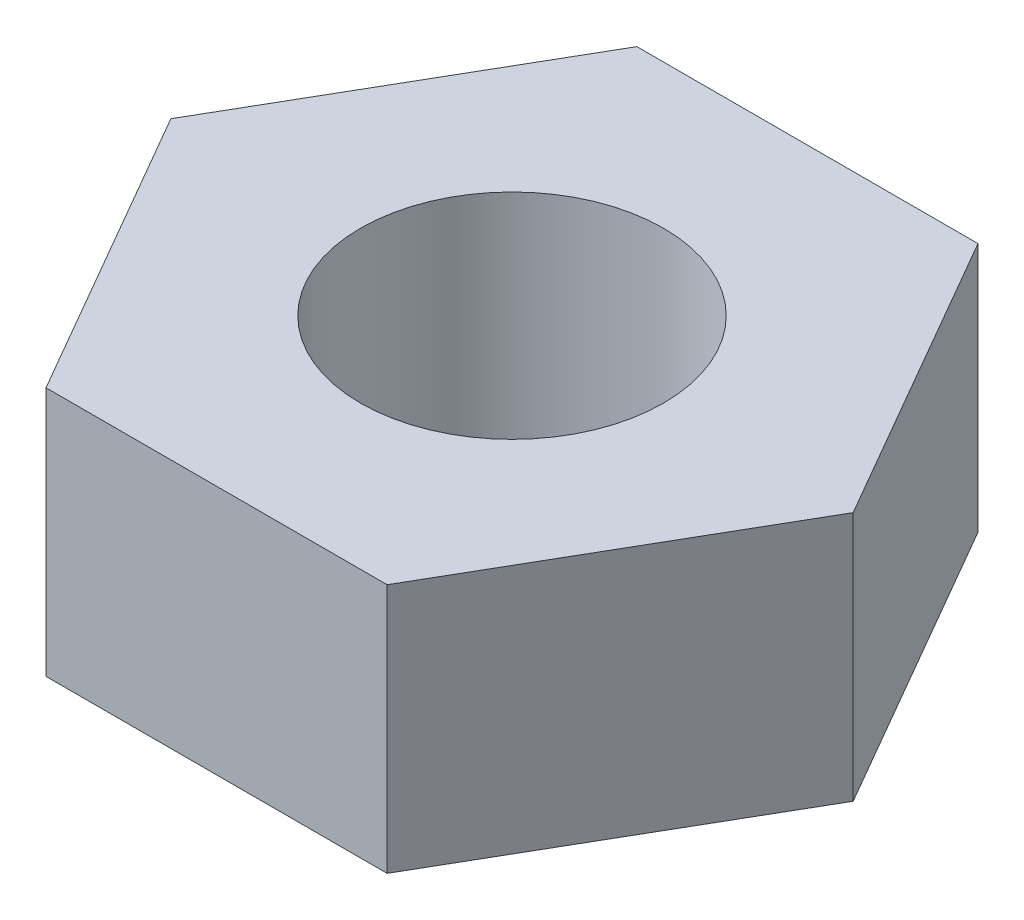
SolidWorks part; units mm, degrees
material "1060 Alloy"
ref_plane "Front Plane" through (0, 0, 0) normal (0, 0, 1) x (1, 0, 0)
ref_plane "Top Plane" through (0, 0, 0) normal (0, 1, 0) x (1, 0, 0)
ref_plane "Right Plane" through (0, 0, 0) normal (1, 0, 0) x (0, 0, -1)
sketch "Sketch1" plane through (0, 0, 0) normal (0, 1, 0) x (1, 0, 0)
  line L1 (2.2517, 0) -> (1.1258, 1.95)
  line L2 (1.1258, 1.95) -> (-1.1258, 1.95)
  line L3 (-1.1258, 1.95) -> (-2.2517, 0)
  line L4 (-2.2517, 0) -> (-1.1258, -1.95)
  line L5 (-1.1258, -1.95) -> (1.1258, -1.95)
  line L6 (1.1258, -1.95) -> (2.2517, 0)
  circle A0 centre (0, 0) radius 1
  circle A1 centre (0, 0) radius 1.95 construction
  point P3 (2.0071, -1.0206)
  dimension "D1" = 2
  dimension "D2" = 3.9
extrude "Boss-Extrude1" add sketch "Sketch1" along normal blind 1.65
